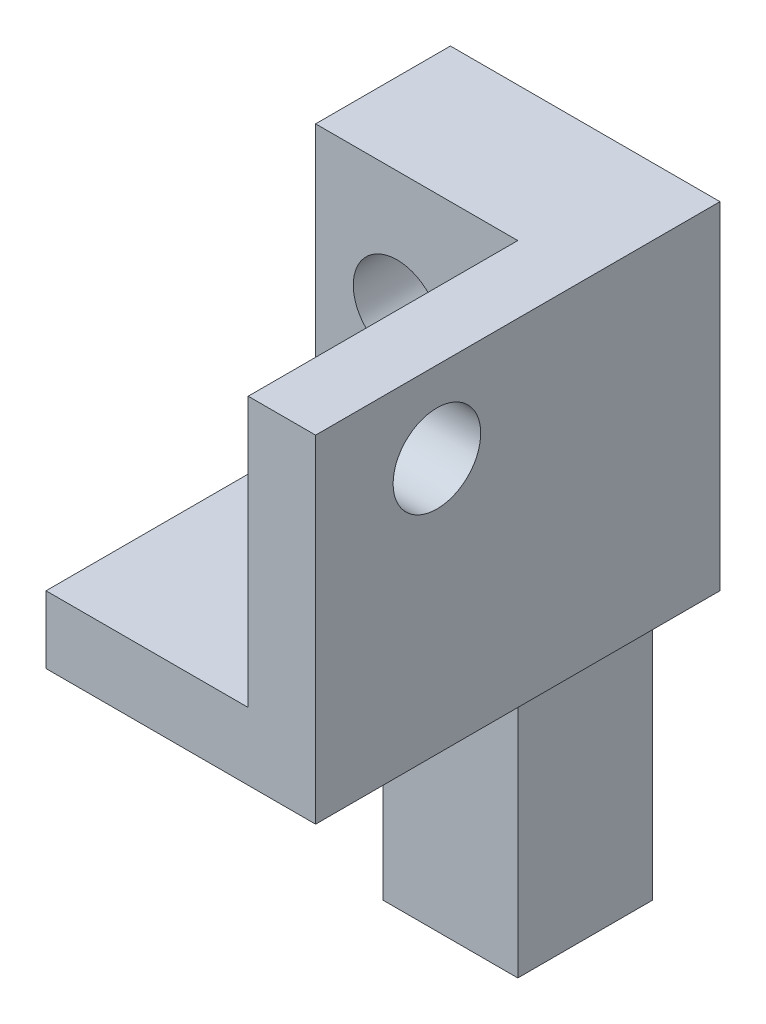
SolidWorks part; units mm, degrees
ref_plane "Front Plane" through (0, 0, 0) normal (0, 0, 1) x (1, 0, 0)
ref_plane "Top Plane" through (0, 0, 0) normal (0, 1, 0) x (1, 0, 0)
ref_plane "Right Plane" through (0, 0, 0) normal (1, 0, 0) x (0, 0, -1)
sketch "Sketch1" plane through (0, 0, 0) normal (1, 0, 0) x (0, 0, -1)
  line L0 (0, -1509.5556) -> (0, 73968.222) construction
  line L1 (0, 0) -> (-10, 0)
  line L2 (-10, 0) -> (-10, -20)
  line L3 (-10, -20) -> (-30, -20)
  line L6 (0, -47.38) -> (0, 0)
  line L7 (-30, -20) -> (-30, -25)
  line L8 (-30, -25) -> (-10, -25)
  line L9 (-10, -25) -> (-10, -47.38)
  line L10 (-10, -47.38) -> (0, -47.38)
  dimension "D1" = 20
  dimension "D2" = 20
  dimension "D3" = 5
  dimension "D4" = 10
  dimension "D5" = 10
  dimension "D6" = 22.38
extrude "Boss-Extrude1" add sketch "Sketch1" along normal blind 10
sketch "Sketch2" plane through (0, 0, 0) normal (-1, 0, 0) x (0, 0, 1)
  line L0 (0, 0) -> (10, 0)
  line L1 (10, 0) -> (10, -20)
  line L2 (10, -20) -> (30, -20)
  line L3 (30, -20) -> (30, -25)
  line L4 (30, -25) -> (0, -25)
  line L5 (0, -47.38) -> (0, 0) construction
  line L6 (0, -25) -> (0, 0)
extrude "Boss-Extrude5" add sketch "Sketch2" along normal blind 5
sketch "Sketch3" plane through (10, 0, 0) normal (1, 0, 0) x (0, 0, -1)
  line L1 (0, 0) -> (-30, 0)
  line L2 (0, 0) -> (0, -25)
  line L3 (0, -25) -> (-30, -25)
  line L4 (-30, 0) -> (-30, -25)
extrude "Boss-Extrude6" add sketch "Sketch3" along normal blind 5
sketch "Sketch4" plane through (0, 0, 0) normal (0, 0, -1) x (-1, 0, 0)
  circle A0 centre (-1.0441, -8.9641) radius 3.25
extrude "Cut-Extrude1" cut sketch "Sketch4" against normal blind 17 and the other way blind 22
sketch "Sketch5" plane through (15, 0, 0) normal (1, 0, 0) x (0, 0, -1)
  circle A0 centre (-21, -6) radius 3.25
extrude "Cut-Extrude2" cut sketch "Sketch5" against normal blind 20 and the other way blind 16
